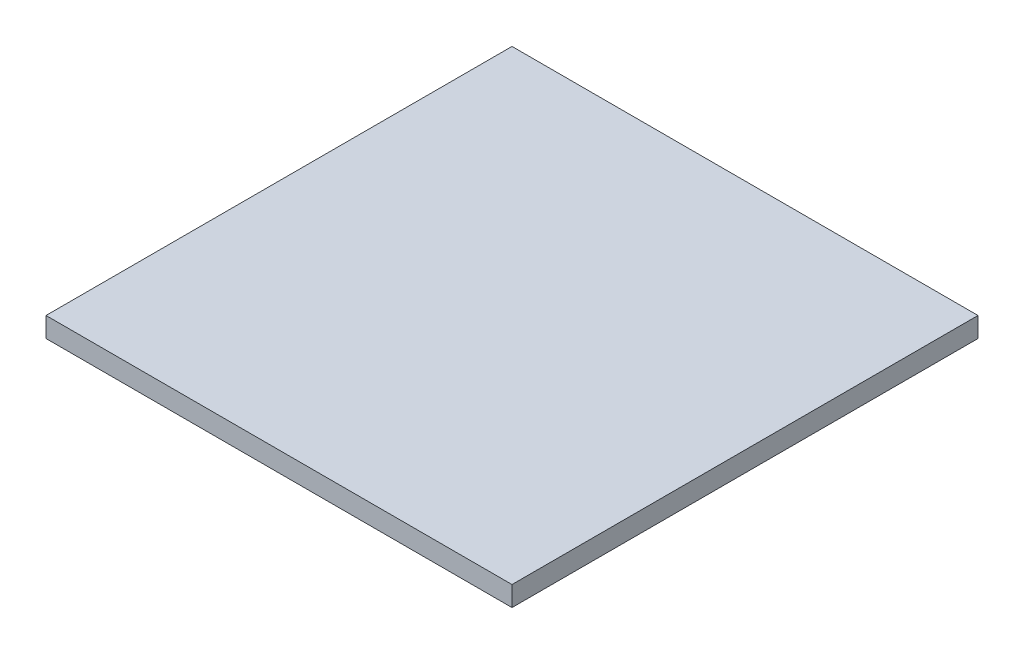
SolidWorks part; units mm, degrees
material "Balsa"
ref_plane "Front Plane" through (0, 0, 0) normal (0, 0, 1) x (1, 0, 0)
ref_plane "Top Plane" through (0, 0, 0) normal (0, 1, 0) x (1, 0, 0)
ref_plane "Right Plane" through (0, 0, 0) normal (1, 0, 0) x (0, 0, -1)
sketch "Sketch1" plane through (0, 0, 0) normal (0, 1, 0) x (1, 0, 0)
  line L1 (-458.4615, 38.8462) -> (-108.4615, 38.8462)
  line L2 (-458.4615, 38.8462) -> (-458.4615, 388.8462)
  line L3 (-458.4615, 388.8462) -> (-108.4615, 388.8462)
  line L4 (-108.4615, 38.8462) -> (-108.4615, 388.8462)
  dimension "D1" = 350
  dimension "D2" = 350
extrude "bottom" add sketch "Sketch1" along normal blind 15
